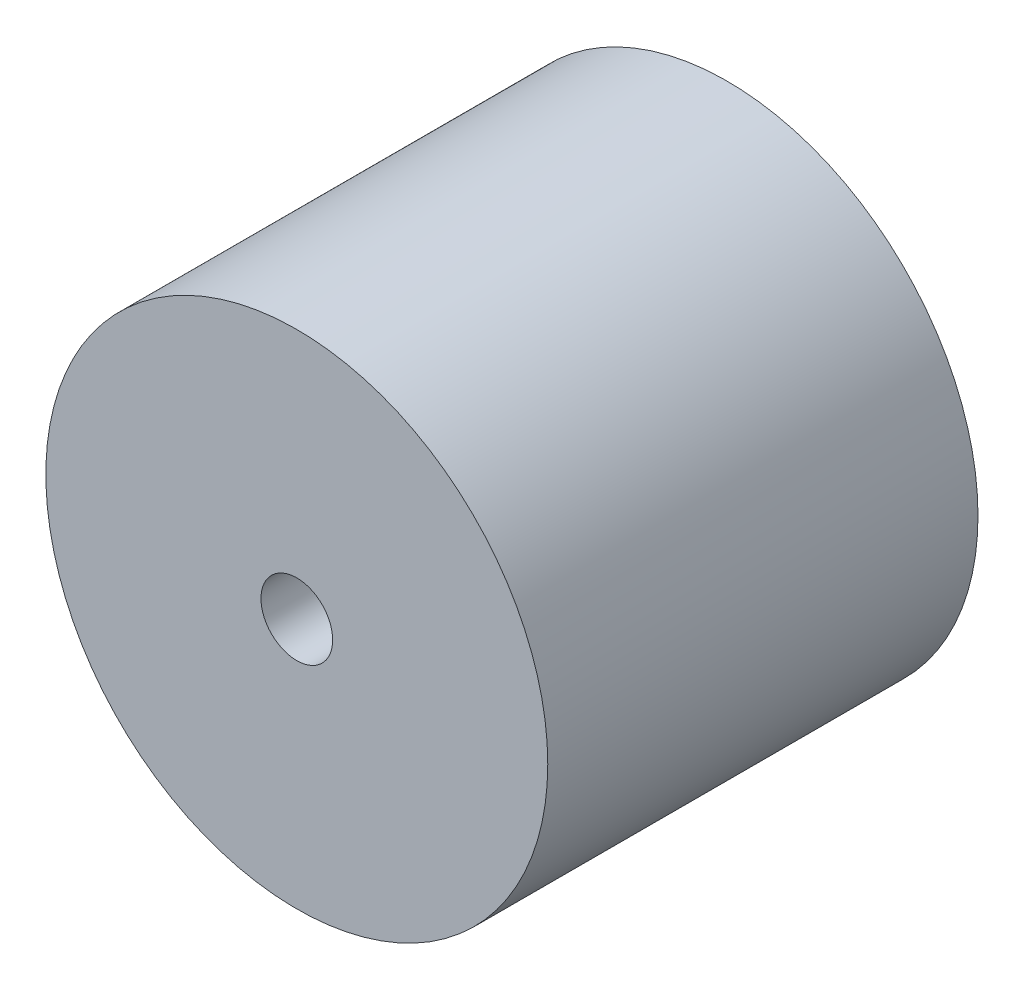
SolidWorks part; units mm, degrees
ref_plane "Plan de face" through (0, 0, 0) normal (0, 0, 1) x (1, 0, 0)
ref_plane "Plan de dessus" through (0, 0, 0) normal (0, 1, 0) x (1, 0, 0)
ref_plane "Plan de droite" through (0, 0, 0) normal (1, 0, 0) x (0, 0, -1)
sketch "Esquisse1" plane through (0, 0, 0) normal (0, 0, 1) x (1, 0, 0)
  circle A0 centre (0, 0) radius 35
  dimension "D1" = 70
extrude "Boss.-Extru.1" add sketch "Esquisse1" along normal blind 60
sketch "Esquisse2" plane through (0, 0, 60) normal (0, 0, 1) x (1, 0, 0)
  circle A0 centre (0, 0) radius 5
  dimension "D1" = 10
extrude "Enlèv. mat.-Extru.1" cut sketch "Esquisse2" against normal blind 60
